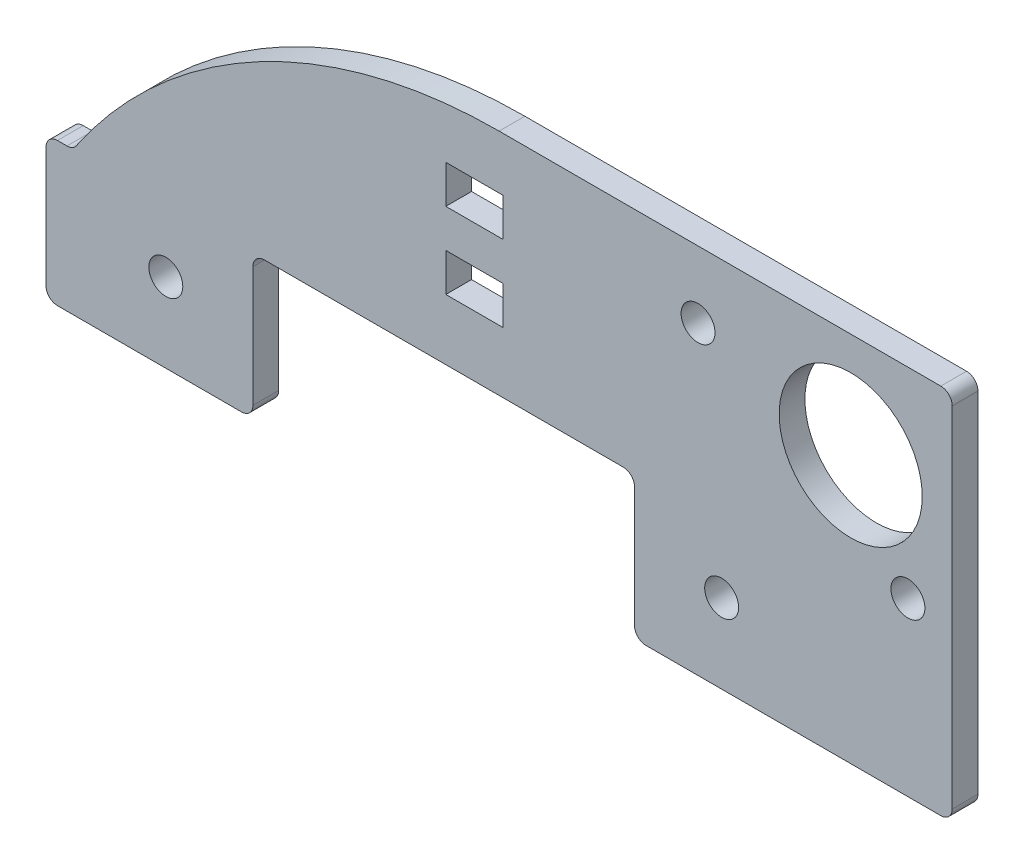
SolidWorks part; units mm, degrees
ref_plane "Front Plane" through (0, 0, 0) normal (0, 0, 1) x (1, 0, 0)
ref_plane "Top Plane" through (0, 0, 0) normal (0, 1, 0) x (1, 0, 0)
ref_plane "Right Plane" through (0, 0, 0) normal (1, 0, 0) x (0, 0, -1)
sketch "Sketch1" plane through (0, 0, 0) normal (0, 0, 1) x (1, 0, 0)
  line L0 (-30.1625, 9.245) -> (30.1625, 9.245)
  line L2 (23.4021, 27.025) -> (23.4021, 25.12) construction
  line L3 (-30.1625, 18.77) -> (-30.1625, 9.245)
  line L5 (0, 9.245) -> (0, 0) construction
  line L6 (14.8131, 14.5155) -> (-22.1869, 14.5155) construction
  line L7 (0, 9.245) -> (0, 14.5155) construction
  line L8 (27.2121, 25.12) -> (13.2421, 25.12) construction
  line L10 (27.2121, 20.675) -> (27.2121, 29.565) construction
  line L12 (13.2421, 20.675) -> (13.2421, 29.565) construction
  line L13 (20.2271, 34.01) -> (20.2271, 25.12) construction
  line L16 (30.1625, 34.01) -> (0, 34.01)
  line L17 (30.1625, 34.01) -> (30.1625, 9.245)
  line L18 (-30.1625, 18.77) -> (-28.3614, 18.77)
  circle A1 centre (23.4021, 27.025) radius 4.7625
  circle A3 centre (-22.1869, 14.5155) radius 1.1303
  circle A4 centre (14.8131, 14.5155) radius 1.1303
  circle A5 centre (27.2121, 20.675) radius 1.1303
  circle A6 centre (13.2421, 29.565) radius 1.1303
  arc A8 (0, 34.01) -> (-28.3614, 18.77) centre (0, 0) ccw
  circle A9 centre (0, 0) radius 31.75 construction
  dimension "D6" = 2.2606
  dimension "D11" = 2.2606
  dimension "D12" = 9.525
  dimension "D15" = 63.5
  dimension "D18" = 7.9756
  dimension "D4" = 37
  dimension "D2" = 9.525
  dimension "D3" = 60.325
  dimension "D5" = 5.2705
  dimension "D7" = 8.89
  dimension "D8" = 13.97
  dimension "D9" = 8.89
  dimension "D10" = 24.765
  dimension "D13" = 1.905
  dimension "D14" = 3.81
  dimension "D16" = 9.245
  dimension "D17" = 9.9354
extrude "Boss-Extrude1" add sketch "Sketch1" along normal blind 1.7145
sketch "Sketch2" plane through (0, 0, 1.7145) normal (0, 0, 1) x (1, 0, 0)
  line L0 (-1.6441, 29.1667) -> (-1.6441, 24.0867) construction
  line L5 (30.1625, 9.245) -> (30.1625, 34.01) construction
  line L11 (-3.5491, 29.1667) -> (0.2609, 29.1667) construction
  line L12 (-3.5491, 30.4367) -> (0.2609, 30.4367)
  line L13 (-3.5491, 30.4367) -> (-3.5491, 27.8967)
  line L14 (-3.5491, 27.8967) -> (0.2609, 27.8967)
  line L15 (0.2609, 30.4367) -> (0.2609, 27.8967)
  line L20 (-3.5491, 24.0867) -> (0.2609, 24.0867) construction
  line L21 (-3.5491, 25.3567) -> (0.2609, 25.3567)
  line L22 (-3.5491, 25.3567) -> (-3.5491, 22.8167)
  line L23 (-3.5491, 22.8167) -> (0.2609, 22.8167)
  line L24 (0.2609, 25.3567) -> (0.2609, 22.8167)
  dimension "D5" = 2.54
  dimension "D6" = 3.81
  dimension "D7" = 5.08
extrude "Cut-Extrude1" cut sketch "Sketch2" against normal up to surface (1.7145 mm away) up to face at (-5.0465, 21.2698, 0)
sketch "Sketch3" plane through (0, 0, 1.7145) normal (0, 0, 1) x (1, 0, 0)
  line L0 (-30.1625, 9.245) -> (30.1625, 9.245) construction
  line L1 (-16.3869, 18.77) -> (9.0131, 18.77)
  line L2 (-16.3869, 18.77) -> (-16.3869, 9.245)
  line L3 (-16.3869, 9.245) -> (9.0131, 9.245)
  line L4 (9.0131, 18.77) -> (9.0131, 9.245)
  line L6 (0, 9.245) -> (0, 14.5155) construction
  line L7 (-22.1869, 14.5155) -> (14.8131, 14.5155) construction
  line L8 (-3.6869, 18.77) -> (-3.6869, 9.245) construction
  circle A0 centre (-22.1869, 14.5155) radius 1.1303 construction
  circle A1 centre (14.8131, 14.5155) radius 1.1303 construction
  point P16 (-3.6869, 14.5155)
  dimension "D1" = 9.525
  dimension "D2" = 25.4
extrude "Cut-Extrude2" cut sketch "Sketch3" against normal up to surface (1.7145 mm away) up to face at (-1.6441, 29.1667, 0)
fillet "Fillet1" radius 0.762 7 edges at (30.1625, 34.01, 0.8573) (30.1625, 9.245, 0.8573) (-30.1625, 9.245, 0.8573) (-28.3614, 18.77, 0.8573) (-30.1625, 18.77, 0.8573) (9.0131, 9.245, 0.8573) (-16.3869, 9.245, 0.8573)
fillet "Fillet2" radius 0.762 2 edges at (9.0131, 18.77, 0.8573) (-16.3869, 18.77, 0.8573)
